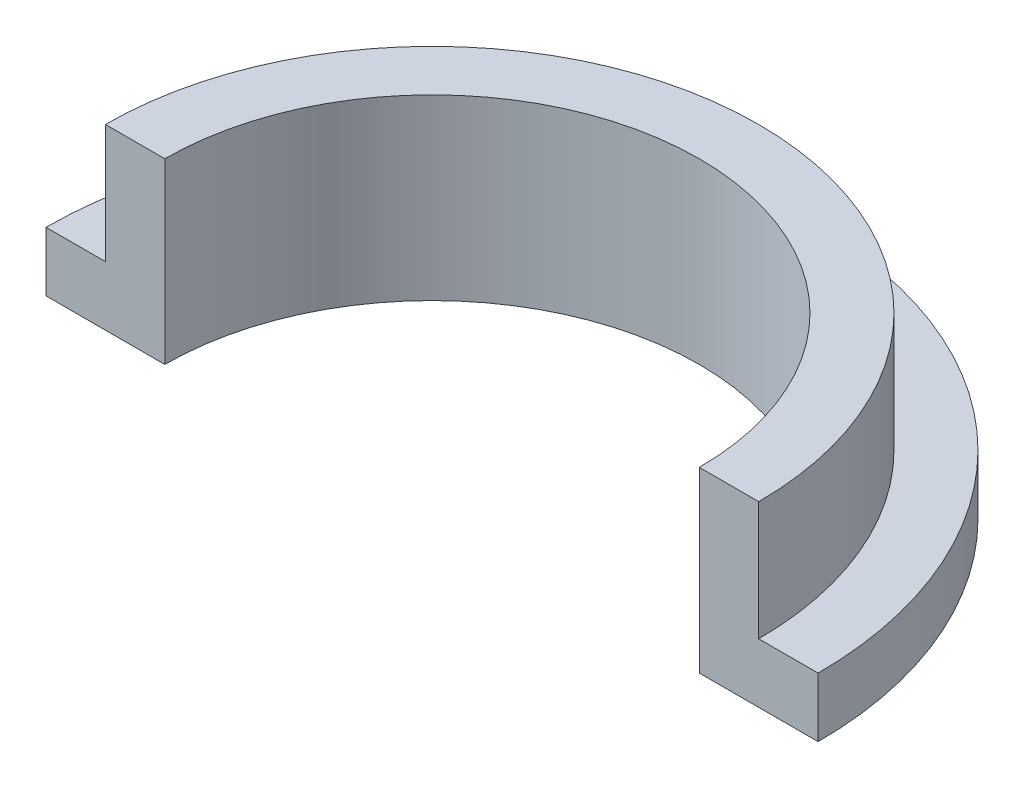
SolidWorks part; units mm, degrees
ref_plane "Front Plane" through (0, 0, 0) normal (0, 0, 1) x (1, 0, 0)
ref_plane "Top Plane" through (0, 0, 0) normal (0, 1, 0) x (1, 0, 0)
ref_plane "Right Plane" through (0, 0, 0) normal (1, 0, 0) x (0, 0, -1)
sketch "Sketch1" plane through (0, 0, 0) normal (0, 1, 0) x (1, 0, 0)
  line L0 (-13, 0) -> (-9, 0)
  line L1 (9, 0) -> (13, 0)
  circle A0 centre (0, 0) radius 12.43 construction
  circle A1 centre (0, 0) radius 9.43 construction
  circle A2 centre (0, 0) radius 13 construction
  circle A3 centre (0, 0) radius 9 construction
  arc A4 (9, 0) -> (-9, 0) centre (0, 0) ccw
  arc A5 (13, 0) -> (-13, 0) centre (0, 0) ccw
  dimension "D1" = 18.86
  dimension "D2" = 24.86
  dimension "D3" = 26
  dimension "D4" = 18
extrude "Boss-Extrude1" add sketch "Sketch1" along normal blind 6
sketch "Sketch2" plane through (0, 6, 0) normal (0, 1, 0) x (1, 0, 0)
  line L2 (-13, 0) -> (-11, 0)
  line L3 (11, 0) -> (13, 0)
  arc A1 (13, 0) -> (-13, 0) centre (0, 0) ccw construction
  arc A2 (11, 0) -> (-11, 0) centre (0, 0) ccw
  arc A3 (11, 0) -> (-11, 0) centre (0, 0) ccw
  arc A4 (13, 0) -> (-13, 0) centre (0, 0) ccw
  dimension "D1" = 2
extrude "Cut-Extrude1" cut sketch "Sketch2" against normal blind 4
